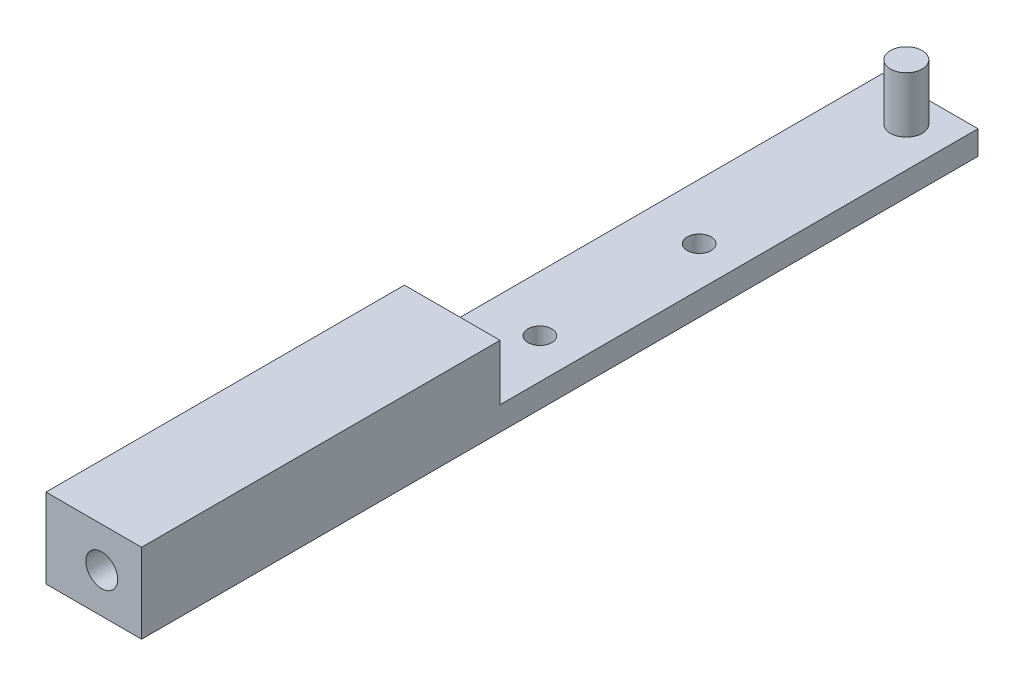
SolidWorks part; units mm, degrees
ref_plane "Front" through (0, 0, 0) normal (0, 0, 1) x (1, 0, 0)
ref_plane "Top" through (0, 0, 0) normal (0, 1, 0) x (1, 0, 0)
ref_plane "Right" through (0, 0, 0) normal (1, 0, 0) x (0, 0, -1)
sketch "Sketch1" plane through (0, 0, 0) normal (0, 1, 0) x (1, 0, 0)
  line L1 (-5, 52.5) -> (5, 52.5)
  line L2 (-5, 52.5) -> (-5, -52.5)
  line L3 (-5, -52.5) -> (5, -52.5)
  line L4 (5, 52.5) -> (5, -52.5)
  line L5 (-5, 52.5) -> (5, -52.5) construction
  line L6 (-5, -52.5) -> (5, 52.5) construction
  point P0 (0, 0)
  dimension "D1" = 105
  dimension "D2" = 10
extrude "Boss-Extrude1" add sketch "Sketch1" along normal blind 10
sketch "Sketch2" plane through (0, 0, 0) normal (1, 0, 0) x (0, 0, -1)
  line L1 (52.5, 16.0957) -> (-7.5, 16.0957)
  line L2 (52.5, 16.0957) -> (52.5, 3)
  line L3 (52.5, 3) -> (-7.5, 3)
  line L4 (-7.5, 16.0957) -> (-7.5, 3)
  line L5 (50, 0) -> (-50, 0) construction
  line L6 (52.5, 10) -> (52.5, 0) construction
  dimension "D1" = 3
  dimension "D2" = 60
  dimension "D3" = 60
extrude "Cut-Extrude1" cut sketch "Sketch2" against normal blind 10 and the other way blind 10
sketch "Sketch3" plane through (0, 3, 0) normal (0, 1, 0) x (1, 0, 0)
  line L0 (0, 60.0963) -> (0, -88.8623) construction
  line L1 (0, -50) -> (0, 50) construction
  line L2 (5, 52.5) -> (-5, 52.5) construction
  circle A0 centre (0, 48.5) radius 2
  dimension "D1" = 4
  dimension "D2" = 4
extrude "Boss-Extrude2" add sketch "Sketch3" along normal blind 7
sketch "Sketch4" plane through (0, 0, 0) normal (0, 1, 0) x (1, 0, 0)
  line L0 (0, -50) -> (0, 50) construction
  line L1 (5, -7.5) -> (-5, -7.5) construction
  circle A0 centre (0, 2.5) radius 1.5
  circle A1 centre (0, 22.5) radius 1.5
  dimension "D1" = 3
  dimension "D3" = 3
  dimension "D2" = 10
  dimension "D4" = 30
extrude "Cut-Extrude2" cut sketch "Sketch4" along normal blind 14
sketch "Sketch5" plane through (0, 0, 52.5) normal (0, 0, 1) x (1, 0, 0)
  line L0 (0, -50) -> (0, 50) construction
  line L1 (-5, 10) -> (5, 10) construction
  circle A0 centre (0, 5) radius 2
  dimension "D1" = 4
  dimension "D2" = 5
extrude "Cut-Extrude3" cut sketch "Sketch5" against normal blind 10
sketch "Sketch6" plane through (-5, 0, 0) normal (-1, 0, 0) x (0, 0, 1)
  line L0 (7.5, 10) -> (52.5, 10)
  line L1 (52.5, 10) -> (52.5, 0)
  line L2 (52.5, 0) -> (-52.5, 0)
  line L3 (-52.5, 0) -> (-52.5, 3)
  line L4 (-52.5, 3) -> (7.5, 3)
  line L5 (7.5, 3) -> (7.5, 10)
extrude "Boss-Extrude3" add sketch "Sketch6" along normal blind 2
